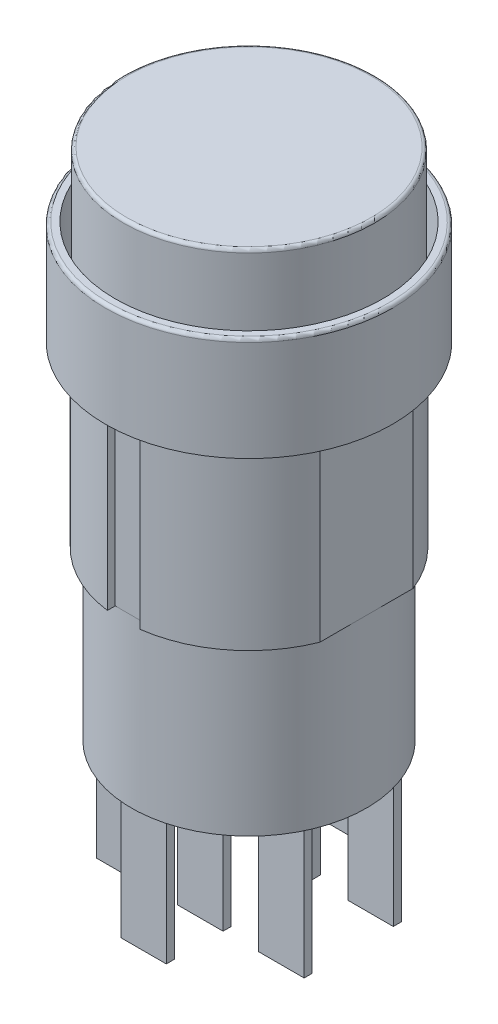
SolidWorks part; units mm, degrees
material "ABS"
ref_plane "Plano frontal" through (0, 0, 0) normal (0, 0, 1) x (1, 0, 0)
ref_plane "Plano superior" through (0, 0, 0) normal (0, 1, 0) x (1, 0, 0)
ref_plane "Plano direito" through (0, 0, 0) normal (1, 0, 0) x (0, 0, -1)
sketch "Esboço2" plane through (0, 0, 0) normal (0, 1, 0) x (1, 0, 0)
  circle A0 centre (0, 0) radius 8.85
  dimension "D1" = 17.7
extrude "Ressalto-extrusão1" add sketch "Esboço2" along normal blind 6.4
sketch "Esboço3" plane through (0, 6.4, 0) normal (0, 1, 0) x (1, 0, 0)
  circle A0 centre (0, 0) radius 8.25
  dimension "D1" = 16.5
extrude "Corte-extrusão1" cut sketch "Esboço3" against normal blind 5
sketch "Esboço4" plane through (0, 1.4, 0) normal (0, 1, 0) x (1, 0, 0)
  circle A0 centre (0, 0) radius 7.75
extrude "Ressalto-extrusão2" add sketch "Esboço4" along normal blind 9
fillet "Filete1" radius 0.2 2 edges at (0, 6.4, 8.85) (0, 10.4, 7.75)
sketch "Esboço5" plane through (0, 0, 0) normal (0, -1, 0) x (1, 0, 0)
  circle A0 centre (0, 0) radius 7.8
extrude "Ressalto-extrusão3" add sketch "Esboço5" along normal blind 11
sketch "Esboço6" plane through (0, -11, 0) normal (0, -1, 0) x (1, 0, 0)
  circle A0 centre (0, 0) radius 7.25
extrude "Ressalto-extrusão4" add sketch "Esboço6" along normal blind 10.3
sketch "Esboço7" plane through (0, -11, 0) normal (0, -1, 0) x (1, 0, 0)
  line L0 (0, 0) -> (13.8862, 0) construction
  line L1 (-7.25, -7.8) -> (-1, -7.8)
  line L2 (-7.25, -7.8) -> (-7.25, 7.8)
  line L3 (-7.25, 7.8) -> (-1, 7.8)
  line L4 (7.25, -7.8) -> (7.25, 7.8)
  line L5 (-7.25, -7.8) -> (7.25, 7.8) construction
  line L6 (-7.25, 7.8) -> (7.25, -7.8) construction
  line L7 (-10.7369, -11.5514) -> (10.7369, -11.5514)
  line L8 (-10.7369, -11.5514) -> (-10.7369, 11.5514)
  line L9 (-10.7369, 11.5514) -> (10.7369, 11.5514)
  line L10 (10.7369, -11.5514) -> (10.7369, 11.5514)
  line L11 (-10.7369, -11.5514) -> (10.7369, 11.5514) construction
  line L12 (-10.7369, 11.5514) -> (10.7369, -11.5514) construction
  line L13 (1, 7.8) -> (7.25, 7.8)
  line L14 (-1, 7.8) -> (-1, 7.25)
  line L15 (-1, 7.25) -> (1, 7.25)
  line L16 (1, 7.8) -> (1, 7.25)
  line L17 (-1, 8.35) -> (1, 7.25) construction
  line L18 (-1, 7.25) -> (1, 8.35) construction
  line L19 (-1, -7.8) -> (-1, -7.25)
  line L20 (1, -7.8) -> (1, -7.25)
  line L21 (-1, -7.25) -> (1, -7.25)
  line L22 (1, -7.8) -> (7.25, -7.8)
  point P0 (0, 0)
  point P6 (0, 0)
  point P11 (0, 7.8)
  dimension "D1" = 14.5
  dimension "D2" = 15.6
  dimension "D3" = 0.55
  dimension "D4" = 2
  dimension "D5" = 0.55
extrude "Corte-extrusão2" cut sketch "Esboço7" against normal blind 11
sketch "Esboço8" plane through (0, -21.3, 0) normal (0, -1, 0) x (1, 0, 0)
  line L0 (-6.4, 3) -> (-6.4, 2.5)
  line L1 (-6.4, 3) -> (-3.6, 3)
  line L2 (-3.6, 3) -> (-3.6, 2.5)
  line L3 (-6.4, 3) -> (-3.6, 2.5) construction
  line L4 (-6.4, 2.5) -> (-3.6, 2.5)
  line L5 (-6.4, 2.5) -> (-3.6, 3) construction
  line L6 (0, 0) -> (0, 6.4831) construction
  line L7 (-1.4, 3) -> (1.4, 3)
  line L8 (-1.4, 3) -> (-1.4, 2.5)
  line L9 (-1.4, 2.5) -> (1.4, 2.5)
  line L10 (1.4, 3) -> (1.4, 2.5)
  line L11 (-1.4, 3) -> (1.4, 2.5) construction
  line L12 (-1.4, 2.5) -> (1.4, 3) construction
  line L13 (0, 0) -> (5.5252, 0) construction
  line L14 (6.4, 2.5) -> (3.6, 3) construction
  line L15 (6.4, 3) -> (3.6, 2.5) construction
  line L16 (6.4, 2.5) -> (3.6, 2.5)
  line L17 (3.6, 3) -> (3.6, 2.5)
  line L18 (6.4, 3) -> (3.6, 3)
  line L19 (6.4, 3) -> (6.4, 2.5)
  line L20 (-1.4, 6.5) -> (-1.4, 6)
  line L21 (1.4, 6.5) -> (1.4, 6)
  line L22 (-1.4, 6) -> (1.4, 6.5) construction
  line L23 (-1.4, 6.5) -> (1.4, 6.5)
  line L24 (-1.4, 6) -> (1.4, 6)
  line L25 (-1.4, 6.5) -> (1.4, 6) construction
  line L26 (-1.4, -6.5) -> (1.4, -6) construction
  line L27 (-1.4, -6) -> (1.4, -6.5) construction
  line L28 (6.4, -3) -> (3.6, -2.5) construction
  line L29 (6.4, -2.5) -> (3.6, -3) construction
  line L30 (-1.4, -2.5) -> (1.4, -3) construction
  line L31 (-1.4, -3) -> (1.4, -2.5) construction
  line L32 (-6.4, -2.5) -> (-3.6, -3) construction
  line L33 (-6.4, -3) -> (-3.6, -2.5) construction
  line L34 (-1.4, -6) -> (1.4, -6)
  line L35 (-1.4, -6.5) -> (1.4, -6.5)
  line L36 (1.4, -6.5) -> (1.4, -6)
  line L37 (-1.4, -6.5) -> (-1.4, -6)
  line L38 (6.4, -3) -> (6.4, -2.5)
  line L39 (6.4, -3) -> (3.6, -3)
  line L40 (3.6, -3) -> (3.6, -2.5)
  line L41 (6.4, -2.5) -> (3.6, -2.5)
  line L42 (1.4, -3) -> (1.4, -2.5)
  line L43 (-1.4, -2.5) -> (1.4, -2.5)
  line L44 (-1.4, -3) -> (-1.4, -2.5)
  line L45 (-1.4, -3) -> (1.4, -3)
  line L46 (-6.4, -2.5) -> (-3.6, -2.5)
  line L47 (-3.6, -3) -> (-3.6, -2.5)
  line L48 (-6.4, -3) -> (-3.6, -3)
  line L49 (-6.4, -3) -> (-6.4, -2.5)
  point P0 (-5, 2.75)
  point P5 (0, 2.75)
  point P18 (5, 2.75)
  point P19 (0, 6.25)
  point P40 (0, -6.25)
  point P41 (5, -2.75)
  point P42 (0, -2.75)
  point P43 (-5, -2.75)
  dimension "D1" = 0.5
  dimension "D2" = 2.8
  dimension "D3" = 2.5
  dimension "D4" = 12.8
  dimension "D5" = 3
extrude "Ressalto-extrusão5" add sketch "Esboço8" along normal blind 8
